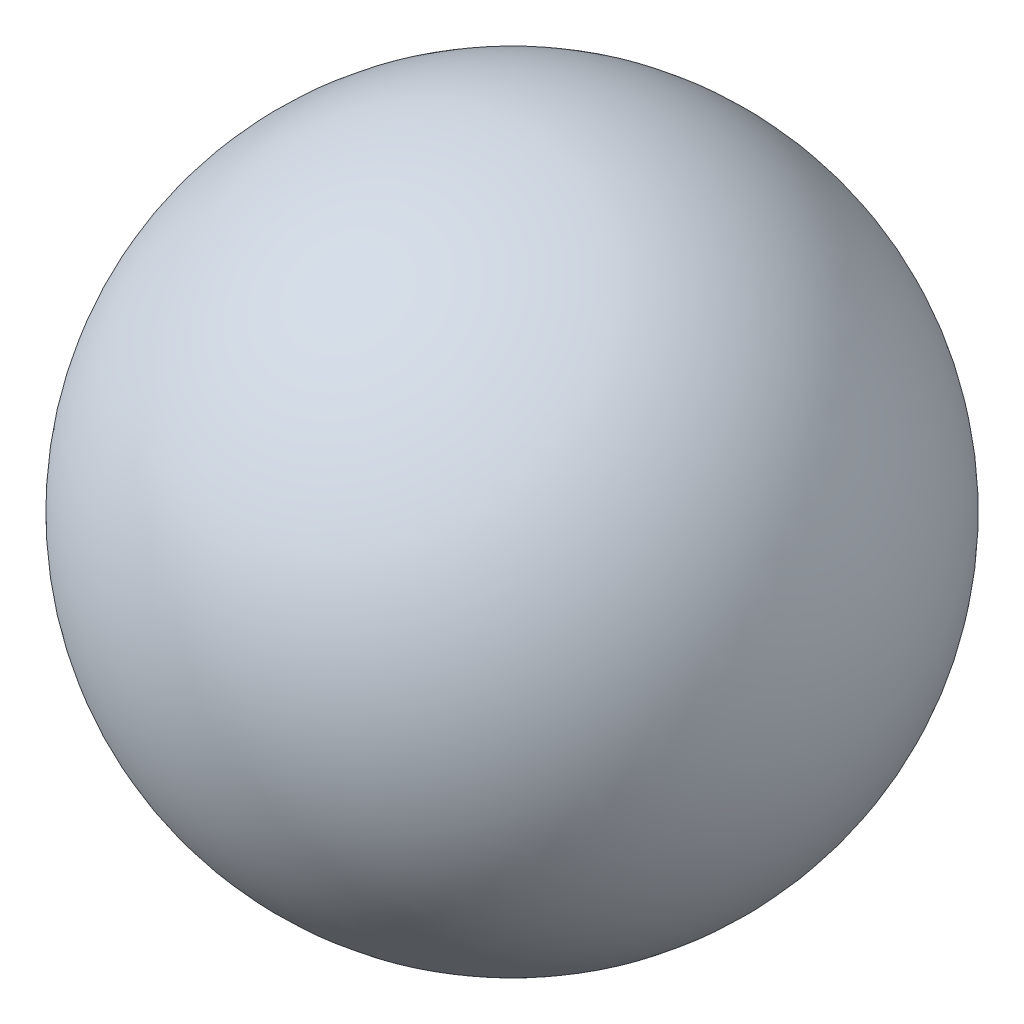
SolidWorks part; units mm, degrees
ref_plane "Front Plane" through (0, 0, 0) normal (0, 0, 1) x (1, 0, 0)
ref_plane "Top Plane" through (0, 0, 0) normal (0, 1, 0) x (1, 0, 0)
ref_plane "Right Plane" through (0, 0, 0) normal (1, 0, 0) x (0, 0, -1)
sketch "Sketch1" plane through (0, 0, 0) normal (0, 0, 1) x (1, 0, 0)
  line L0 (0, 3.6578) -> (0, -4.9422)
  arc A0 (0, -4.9422) -> (0, 3.6578) centre (0, -0.6422) ccw
  dimension "D1" = 8.6
revolve "Revolve3" add sketch "Sketch1" angle 360 about L0
